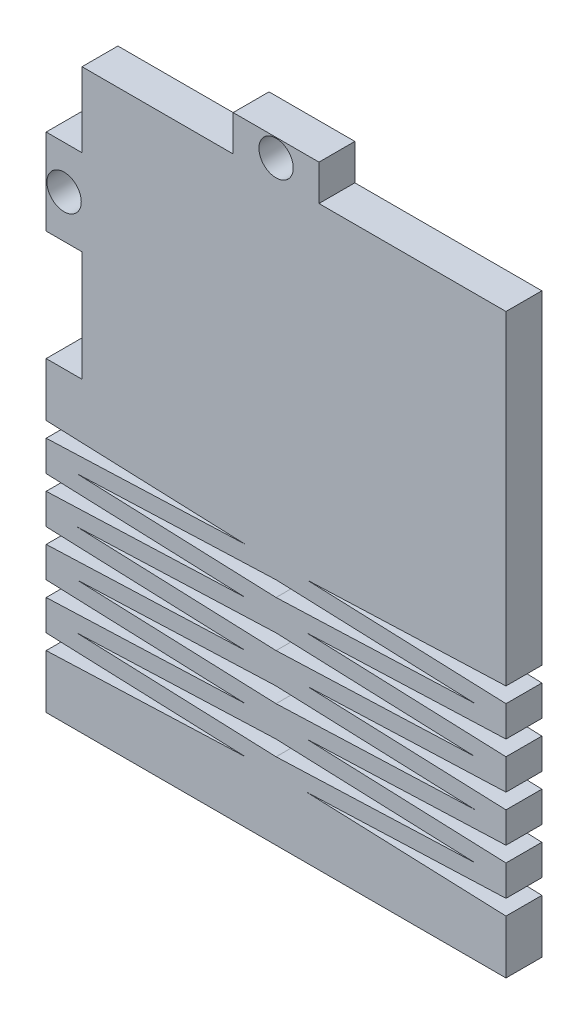
SolidWorks part; units mm, degrees
ref_plane "Front Plane" through (0, 0, 0) normal (0, 0, 1) x (1, 0, 0)
ref_plane "Top Plane" through (0, 0, 0) normal (0, 1, 0) x (1, 0, 0)
ref_plane "Right Plane" through (0, 0, 0) normal (1, 0, 0) x (0, 0, -1)
sketch "Sketch1" plane through (0, 0, 0) normal (0, 0, 1) x (1, 0, 0)
  line L0 (2.9718, 22.4282) -> (15.494, 22.4282)
  line L1 (0, 0) -> (38.1, 0)
  line L2 (0, 0) -> (0, 25.4)
  line L3 (0, 25.4) -> (38.1, 25.4)
  line L4 (38.1, 0) -> (38.1, 25.4)
  line L5 (15.494, 22.4282) -> (15.494, 25.4)
  line L6 (15.494, 25.4) -> (22.606, 25.4)
  line L7 (22.606, 25.4) -> (22.606, 22.4282)
  line L8 (22.606, 22.4282) -> (38.1, 22.4282)
  line L9 (2.9718, 0) -> (2.9718, 9.144)
  line L10 (2.9718, 9.144) -> (0, 9.144)
  line L11 (0, 9.144) -> (0, 16.256)
  line L12 (0, 16.256) -> (2.9718, 16.256)
  line L13 (2.9718, 16.256) -> (2.9718, 22.4282)
  line L14 (0, -5.08) -> (38.1, -5.08) construction
  line L15 (0, 0) -> (38.1, 0)
  line L16 (0, 0) -> (0, -25.4)
  line L17 (0, -25.4) -> (38.1, -25.4)
  line L18 (38.1, 0) -> (38.1, -25.4)
  line L19 (0, -4.445) -> (16.51, -5.08)
  line L20 (19.05, -25.4) -> (19.05, 0) construction
  line L21 (0, -5.715) -> (16.51, -5.08)
  line L22 (38.1, -6.985) -> (0, -6.985) construction
  line L23 (2.54, -6.985) -> (19.05, -6.35)
  line L24 (38.1, -5.715) -> (21.59, -5.08)
  line L25 (38.1, -4.445) -> (21.59, -5.08)
  line L27 (35.56, -6.985) -> (19.05, -6.35)
  line L29 (2.54, -6.985) -> (19.05, -7.62)
  line L30 (0, -8.255) -> (16.51, -8.89)
  line L31 (0, -9.525) -> (16.51, -8.89)
  line L32 (38.1, -9.525) -> (21.59, -8.89)
  line L33 (0, -8.89) -> (38.1, -8.89) construction
  line L34 (38.1, -8.255) -> (21.59, -8.89)
  line L35 (35.56, -6.985) -> (19.05, -7.62)
  line L36 (0, -12.065) -> (16.51, -12.7)
  line L37 (0, -13.335) -> (16.51, -12.7)
  line L38 (0, -12.7) -> (38.1, -12.7) construction
  line L39 (38.1, -13.335) -> (21.59, -12.7)
  line L40 (38.1, -12.065) -> (21.59, -12.7)
  line L41 (35.56, -10.795) -> (19.05, -10.16)
  line L42 (35.56, -10.795) -> (19.05, -11.43)
  line L43 (2.54, -10.795) -> (19.05, -11.43)
  line L44 (38.1, -10.795) -> (0, -10.795) construction
  line L45 (2.54, -10.795) -> (19.05, -10.16)
  line L46 (0, -9.525) -> (16.51, -8.89)
  line L47 (38.1, -9.525) -> (21.59, -8.89)
  line L48 (38.1, -19.685) -> (21.59, -20.32)
  line L49 (38.1, -20.955) -> (21.59, -20.32)
  line L50 (0, -20.955) -> (16.51, -20.32)
  line L51 (0, -20.32) -> (38.1, -20.32) construction
  line L52 (0, -19.685) -> (16.51, -20.32)
  line L53 (2.54, -18.415) -> (19.05, -19.05)
  line L54 (38.1, -18.415) -> (0, -18.415) construction
  line L55 (2.54, -18.415) -> (19.05, -17.78)
  line L56 (0, -17.145) -> (16.51, -16.51)
  line L57 (0, -16.51) -> (38.1, -16.51) construction
  line L58 (0, -15.875) -> (16.51, -16.51)
  line L59 (38.1, -17.145) -> (21.59, -16.51)
  line L60 (38.1, -15.875) -> (21.59, -16.51)
  line L61 (35.56, -14.605) -> (19.05, -15.24)
  line L62 (2.54, -14.605) -> (19.05, -15.24)
  line L63 (38.1, -14.605) -> (0, -14.605) construction
  line L64 (2.54, -14.605) -> (19.05, -13.97)
  line L65 (35.56, -14.605) -> (19.05, -13.97)
  line L66 (38.1, -13.335) -> (21.59, -12.7)
  line L67 (0, -13.335) -> (16.51, -12.7)
  line L68 (35.56, -18.415) -> (19.05, -17.78)
  line L69 (35.56, -18.415) -> (19.05, -19.05)
  circle A0 centre (19.05, 23.9141) radius 1.4224
  circle A1 centre (1.4859, 12.7) radius 1.4224
  point P5 (0, 0)
  point P37 (33.1162, -6.985)
  point P38 (28.057, -6.985)
  point P39 (19.05, -7.6017)
  point P40 (19.05, 25.4)
  point P42 (0, 12.7)
  dimension "D9" = 2.8448
  dimension "D10" = 2.8448
  dimension "D1" = 38.1
  dimension "D2" = 25.4
  dimension "D3" = 2.9718
  dimension "D4" = 2.9718
  dimension "D5" = 15.494
  dimension "D6" = 9.144
  dimension "D7" = 7.112
  dimension "D8" = 7.112
  dimension "D11" = 1.4859
  dimension "D12" = 1.4859
  dimension "D13" = 25.4
  dimension "D14" = 2.54
  dimension "D15" = 0.635
  dimension "D16" = 0.635
  dimension "D17" = 5.08
  dimension "D18" = 1.27
  dimension "D19" = 2.54
extrude "Boss-Extrude7" add sketch "Sketch1" along normal blind 2.9718 contours L60 L18 L39 L40 L32 L34 L24 L25 L1 L16 L19 L21 L30 L31 L36 L37 L58 L56 L52 L50 L17 L49 L48 L59 L65 L61 L62 L64 L27 L35 L29 L23 L43 L45 L41 L42 | L13 L12 L2 L10 L9 L1 L4 L8 L7 L3 L5 L0 A1 A0
